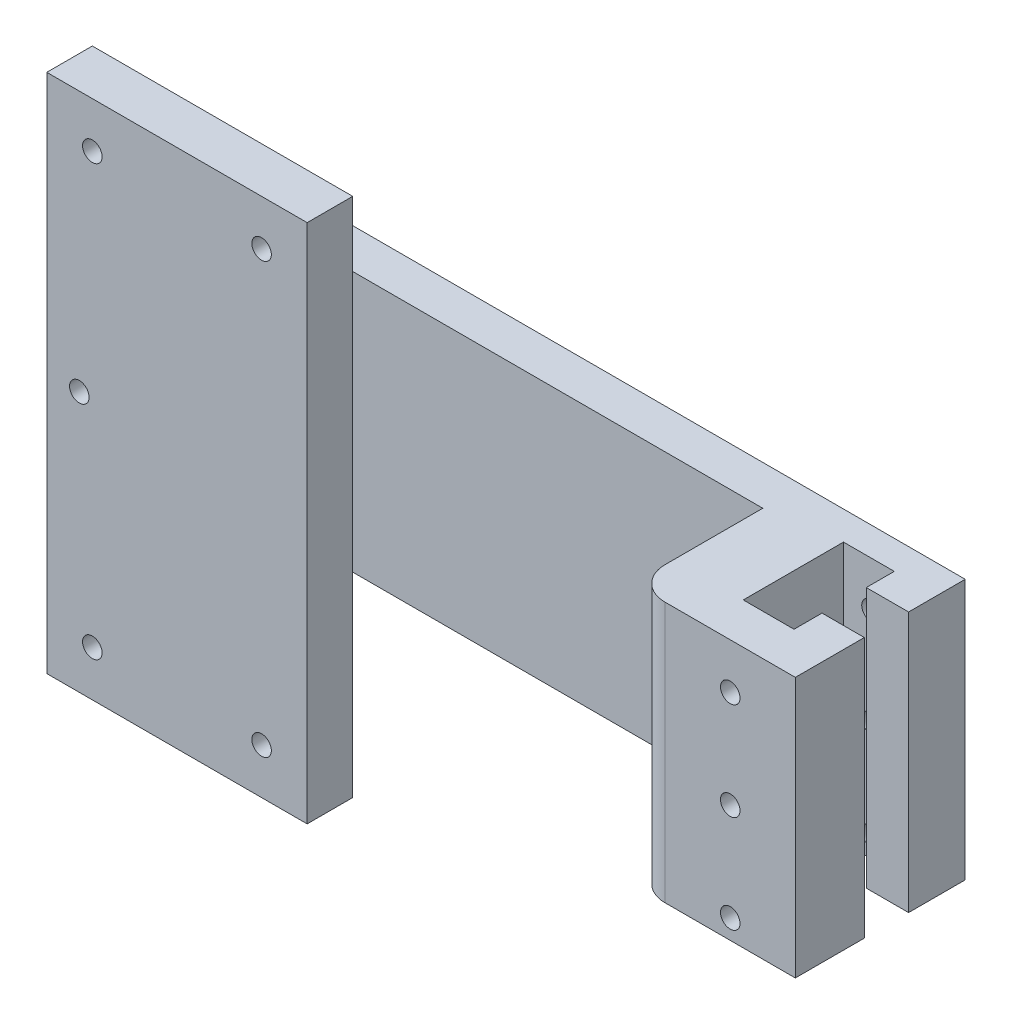
SolidWorks part; units mm, degrees
ref_plane "Front Plane" through (0, 0, 0) normal (0, 0, 1) x (1, 0, 0)
ref_plane "Top Plane" through (0, 0, 0) normal (0, 1, 0) x (1, 0, 0)
ref_plane "Right Plane" through (0, 0, 0) normal (1, 0, 0) x (0, 0, -1)
sketch "Sketch1" plane through (0, 0, 0) normal (0, 0, 1) x (1, 0, 0)
  line L1 (-49.2336, 13.3942) -> (60.7664, 13.3942)
  line L2 (-49.2336, 13.3942) -> (-49.2336, -26.6058)
  line L3 (-49.2336, -26.6058) -> (60.7664, -26.6058)
  line L4 (60.7664, 13.3942) -> (60.7664, -26.6058)
  dimension "D1" = 40
  dimension "D2" = 110
extrude "Boss-Extrude1" add sketch "Sketch1" along normal blind 26.1
sketch "Sketch2" plane through (0, 13.3942, 0) normal (0, 1, 0) x (1, 0, 0)
  line L0 (60.7664, -26.1) -> (60.7664, 0) construction
  line L1 (60.7664, -15.5) -> (54.2664, -15.5)
  line L2 (60.7664, -15.5) -> (60.7664, -8.7)
  line L3 (60.7664, -8.7) -> (54.2664, -8.7)
  line L4 (54.2664, -15.5) -> (54.2664, -8.7)
  line L5 (46.4664, -19.8) -> (54.2664, -19.8)
  line L6 (46.4664, -19.8) -> (46.4664, -4.4)
  line L7 (46.4664, -4.4) -> (54.2664, -4.4)
  line L8 (54.2664, -19.8) -> (54.2664, -4.4)
  line L9 (60.7664, 0) -> (-49.2336, 0) construction
  line M4 (60.7664, -26.1) -> (60.7664, 0)
  dimension "D1" = 0
  dimension "D2" = 0
  dimension "D3" = 4.3
  dimension "D4" = 4.3
  dimension "D5" = 6.8
  dimension "D6" = 8.7
  dimension "D7" = 7.8
  dimension "D8" = 6.5
extrude "Cut-Extrude1" cut sketch "Sketch2" against normal through all contours L4 L1 L3 M4 | L5 L8 L4 L7 L6
sketch "Sketch3" plane through (0, 0, 26.1) normal (0, 0, 1) x (1, 0, 0)
  line L0 (60.7664, -26.6058) -> (60.7664, 13.3942) construction
  line L1 (35.7664, 13.3942) -> (-29.2336, 13.3942)
  line L2 (35.7664, 13.3942) -> (35.7664, -26.6058)
  line L3 (35.7664, -26.6058) -> (-29.2336, -26.6058)
  line L4 (-29.2336, 13.3942) -> (-29.2336, -26.6058)
  line L5 (60.7664, 13.3942) -> (-49.2336, 13.3942) construction
  line L6 (-49.2336, -26.6058) -> (60.7664, -26.6058) construction
  line L7 (-49.2336, 13.3942) -> (-49.2336, -26.6058) construction
  dimension "D1" = 25
  dimension "D2" = 0
  dimension "D3" = 0
  dimension "D4" = 20
extrude "Cut-Extrude2" cut sketch "Sketch3" against normal blind 20
sketch "Sketch5" plane through (0, 0, 26.1) normal (0, 0, 1) x (1, 0, 0)
  line L0 (60.7664, 13.3942) -> (35.7664, 13.3942) construction
  line L1 (35.7664, -26.6058) -> (35.7664, 13.3942) construction
  circle A0 centre (50.7664, 6.3942) radius 1.5
  circle A1 centre (50.7664, -8.6058) radius 1.5
  circle A2 centre (50.7664, -23.6058) radius 1.5
  dimension "D1" = 3
  dimension "D2" = 7
  dimension "D3" = 15
  dimension "D4" = 15
  dimension "D5" = 3
  dimension "D6" = 15
  dimension "D7" = 15
  dimension "D8" = 3
  dimension "D9" = 15
extrude "Cut-Extrude3" cut sketch "Sketch5" against normal through all
fillet "Fillet1" radius 5 1 edges at (35.7664, -6.6058, 26.1)
sketch "Sketch8" plane through (0, 0, 26.1) normal (0, 0, 1) x (1, 0, 0)
  line L0 (-29.2336, 13.3942) -> (-29.2336, -26.6058) construction
  line L1 (-29.2336, 13.3942) -> (-49.2336, 13.3942)
  line L2 (-29.2336, 13.3942) -> (-29.2336, -26.6058)
  line L3 (-29.2336, -26.6058) -> (-49.2336, -26.6058)
  line L4 (-49.2336, 13.3942) -> (-49.2336, -26.6058)
  line L5 (-29.2336, 13.3942) -> (-49.2336, 13.3942) construction
  line L6 (-49.2336, -26.6058) -> (-29.2336, -26.6058) construction
  line L7 (-49.2336, 13.3942) -> (-49.2336, -26.6058) construction
  dimension "D1" = 0
  dimension "D2" = 0
  dimension "D3" = 0
  dimension "D4" = 0
extrude "Cut-Extrude4" cut sketch "Sketch8" against normal blind 3
sketch "Sketch9" plane through (0, 0, 23.1) normal (0, 0, 1) x (1, 0, 0)
  line L0 (60.7664, -26.6058) -> (60.7664, 13.3942) construction
  line L1 (-17.2336, 33.3942) -> (-57.2336, 33.3942)
  line L2 (-17.2336, 33.3942) -> (-17.2336, -46.6058)
  line L3 (-17.2336, -46.6058) -> (-57.2336, -46.6058)
  line L4 (-57.2336, 33.3942) -> (-57.2336, -46.6058)
  line L5 (-29.2336, 13.3942) -> (-49.2336, 13.3942) construction
  line L6 (-49.2336, -26.6058) -> (-29.2336, -26.6058) construction
  dimension "D1" = 78
  dimension "D2" = 40
  dimension "D3" = 20
  dimension "D4" = 20
extrude "Boss-Extrude3" add sketch "Sketch9" against normal blind 7
sketch "Sketch10" plane through (0, 0, 23.1) normal (0, 0, 1) x (1, 0, 0)
  line L0 (-17.2336, -46.6058) -> (-17.2336, 33.3942) construction
  line L1 (-17.2336, 33.3942) -> (-57.2336, 33.3942) construction
  line L2 (-57.2336, 33.3942) -> (-57.2336, -46.6058) construction
  line L3 (-57.2336, -46.6058) -> (-17.2336, -46.6058) construction
  circle A0 centre (-24.2336, 26.3942) radius 1.5
  circle A1 centre (-50.2336, 26.3942) radius 1.5
  circle A2 centre (-52.2336, -6.6058) radius 1.5
  circle A3 centre (-50.2336, -39.6058) radius 1.5
  circle A4 centre (-24.2336, -39.6058) radius 1.5
  dimension "D1" = 7
  dimension "D2" = 7
  dimension "D3" = 3
  dimension "D4" = 7
  dimension "D5" = 7
  dimension "D6" = 3
  dimension "D7" = 5
  dimension "D8" = 40
  dimension "D9" = 3
  dimension "D10" = 3
  dimension "D11" = 7
  dimension "D12" = 7
  dimension "D13" = 7
  dimension "D14" = 3
  dimension "D15" = 7
extrude "Cut-Extrude5" cut sketch "Sketch10" against normal blind 7
